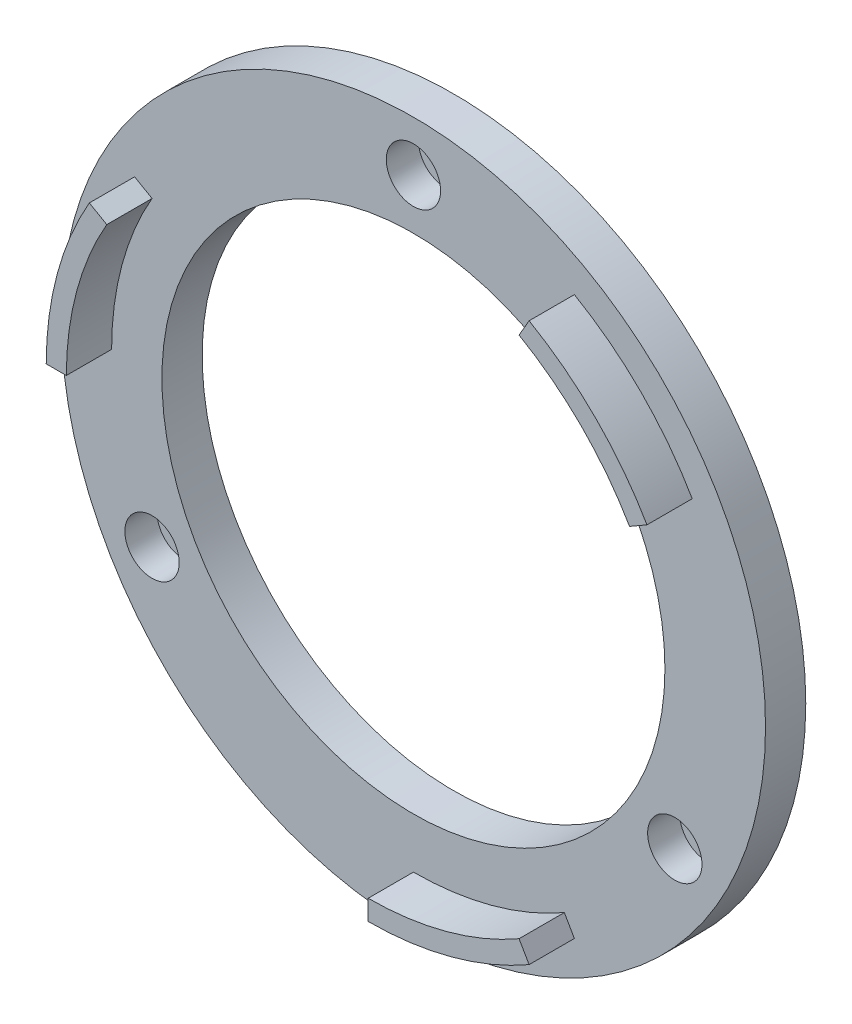
SolidWorks part; units mm, degrees
ref_plane "Front Plane" through (0, 0, 0) normal (0, 0, 1) x (1, 0, 0)
ref_plane "Top Plane" through (0, 0, 0) normal (0, 1, 0) x (1, 0, 0)
ref_plane "Right Plane" through (0, 0, 0) normal (1, 0, 0) x (0, 0, -1)
sketch "Sketch1" plane through (0, 0, 0) normal (0, 0, 1) x (1, 0, 0)
  circle A0 centre (0, 0) radius 30
  circle A1 centre (0, 0) radius 35
  circle A2 centre (0, 0) radius 25
  dimension "D1" = 5
  dimension "D2" = 5
extrude "Boss-Extrude1" add sketch "Sketch1" along normal blind 4 contours A1 A0 | A0 A2
sketch "Sketch2" plane through (0, 0, 0) normal (0, 0, -1) x (-1, 0, 0)
  circle A0 centre (0, 0) radius 30
  circle A1 centre (0, 30) radius 3.9
  circle A5 centre (25.9808, -15) radius 3.9
  circle A6 centre (-25.9808, -15) radius 3.9
  point P12 (0, 0)
  point P14 (0, 0)
  dimension "D1" = 3
extrude "Boss-Extrude2" add sketch "Sketch2" along normal blind 7.1 contours A1 | A6 | A5
sketch "Sketch3" plane through (0, 0, -7.1) normal (0, 0, -1) x (-1, 0, 0)
  circle A0 centre (0, 30) radius 1.6
  circle A4 centre (25.9808, -15) radius 1.6
  circle A5 centre (-25.9808, -15) radius 1.6
  point P10 (0, 0)
  point P12 (0, 0)
  dimension "D1" = 3
extrude "Cut-Extrude1" cut sketch "Sketch3" against normal blind 15
sketch "Sketch4" plane through (0, 0, 4) normal (0, 0, 1) x (1, 0, 0)
  circle A0 centre (0, 30) radius 2.7
  circle A4 centre (25.9808, -15) radius 2.7
  circle A5 centre (-25.9808, -15) radius 2.7
  point P10 (0, 0)
  point P11 (0, 0)
  dimension "D1" = 3
extrude "Cut-Extrude2" cut sketch "Sketch4" against normal blind 3.2
sketch "Sketch6" plane through (0, 0, 4) normal (0, 0, 1) x (1, 0, 0)
  line L0 (32, 0) -> (-32, 0)
  line L1 (0, 0) -> (16, 27.7128)
  line L2 (0, 0) -> (27.7128, 16)
  circle A0 centre (0, 0) radius 32
  circle A1 centre (0, 0) radius 30
  point P7 (0, 0)
extrude "Boss-Extrude3" add sketch "Sketch6" along normal blind 4.5 contours A1 L2 A0 L1
sketch "Sketch7" plane through (0, 0, 4) normal (0, 0, 1) x (1, 0, 0)
  line L0 (16, -27.7128) -> (15, -25.9808)
  line L1 (0, -30) -> (0, -32)
  line L2 (25.9808, 15) -> (27.7128, 16)
  line L3 (16, 27.7128) -> (15, 25.9808)
  line L4 (25.9808, 15) -> (27.7128, 16)
  line L5 (16, 27.7128) -> (15, 25.9808)
  line L6 (-32, 0) -> (-30, 0)
  line L7 (-25.9808, 15) -> (-27.7128, 16)
  arc A0 (0, -30) -> (15, -25.9808) centre (0, 0) ccw
  arc A1 (0, -32) -> (16, -27.7128) centre (0, 0) ccw
  arc A2 (25.9808, 15) -> (15, 25.9808) centre (0, 0) ccw
  arc A3 (27.7128, 16) -> (16, 27.7128) centre (0, 0) ccw
  arc A4 (25.9808, 15) -> (15, 25.9808) centre (0, 0) ccw
  arc A5 (27.7128, 16) -> (16, 27.7128) centre (0, 0) ccw
  arc A6 (-25.9808, 15) -> (-30, 0) centre (0, 0) ccw
  arc A7 (-27.7128, 16) -> (-32, 0) centre (0, 0) ccw
  point P17 (0, 0)
  dimension "D1" = 0
  dimension "D2" = 3
extrude "Boss-Extrude4" add sketch "Sketch7" along normal blind 4.5 contours A4 L5 A5 L4 | L6 A6 L7 A7 | L0 A0 L1 A1
sketch "Sketch8" plane through (0, 0, 0) normal (0, 0, -1) x (-1, 0, 0)
  circle A0 centre (0, 30) radius 3.9
  circle A1 centre (25.9808, -15) radius 3.9
  circle A2 centre (-25.9808, -15) radius 3.9
extrude "Cut-Extrude3" cut sketch "Sketch8" along normal blind 12.5
